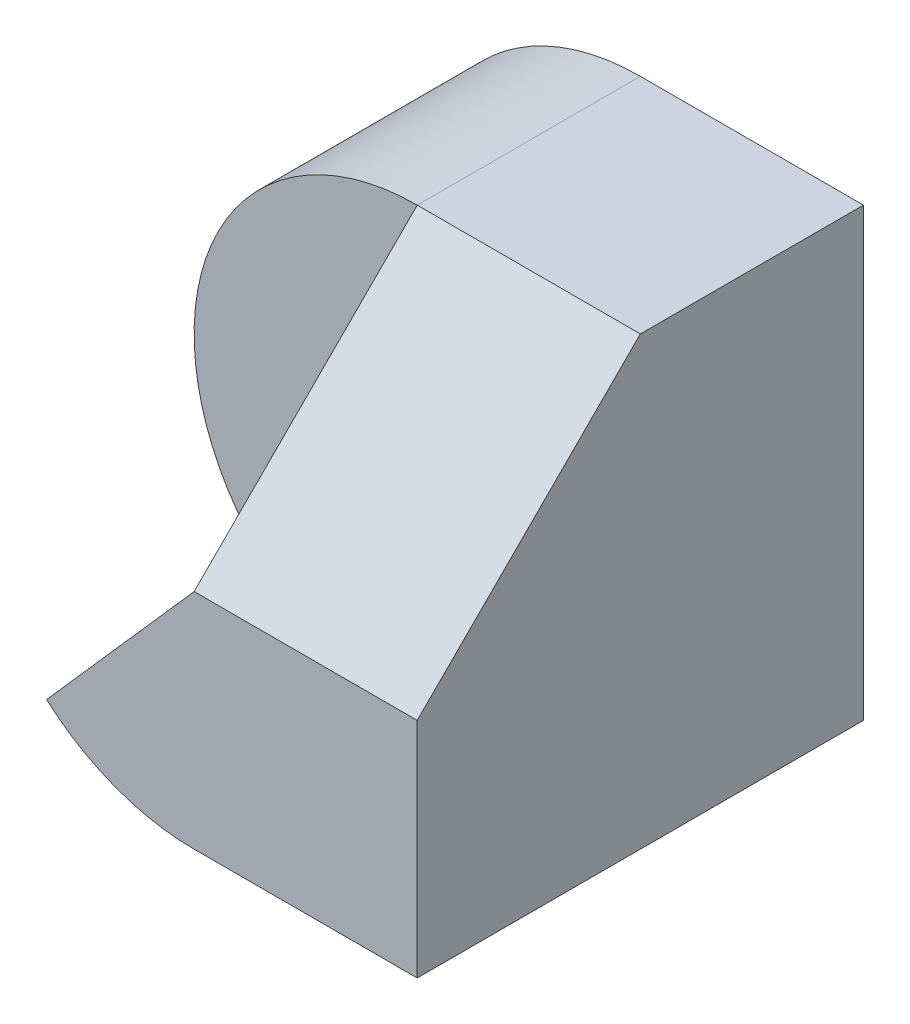
SolidWorks part; units mm, degrees
ref_plane "Front Plane" through (0, 0, 0) normal (0, 0, 1) x (1, 0, 0)
ref_plane "Top Plane" through (0, 0, 0) normal (0, 1, 0) x (1, 0, 0)
ref_plane "Right Plane" through (0, 0, 0) normal (1, 0, 0) x (0, 0, -1)
sketch "Sketch1" plane through (0, 0, 0) normal (0, 0, 1) x (1, 0, 0)
  line L1 (0, 0) -> (40, 0)
  line L2 (0, 0) -> (0, 40)
  line L3 (0, 40) -> (40, 40)
  line L4 (40, 0) -> (40, 40)
  dimension "D1" = 40
  dimension "D2" = 40
extrude "Boss-Extrude1" add sketch "Sketch1" along normal blind 40
sketch "Sketch2" plane through (0, 0, 40) normal (0, 0, 1) x (1, 0, 0)
  line L0 (0, 40) -> (0, 0) construction
  line L1 (40, 40) -> (0, 40) construction
  line L2 (20, 40) -> (0, 40)
  line L3 (0, 40) -> (0, 0)
  line L4 (0, 0) -> (20, 0)
  circle A0 centre (20, 20) radius 20
  line M1 (0, 40) -> (0, 0)
  line M2 (0, 0) -> (40, 0)
  line M4 (40, 40) -> (0, 40)
  dimension "D1" = 40
  dimension "D2" = 20
  dimension "D3" = 20
  dimension "D4" = 20
  dimension "D5" = 20
  dimension "D6" = 20
extrude "Cut-Extrude1" cut sketch "Sketch2" against normal blind 40 contours A0 M4 M1 | A0 L3 M2
ref_plane "Plane1" through (0, 40, 0) normal (0, 1, 0) x (1, 0, 0)
sketch "Sketch3" plane through (0, 40, 0) normal (0, 1, 0) x (1, 0, 0)
  line L1 (0, -40) -> (5, -40)
  line L2 (0, -40) -> (0, -20)
  line L3 (0, -20) -> (5, -20)
  line L4 (5, -40) -> (5, -20)
  dimension "D1" = 5
  dimension "D2" = 20
  dimension "D3" = 40
  dimension "D4" = 0
extrude "Cut-Extrude3" cut sketch "Sketch3" against normal blind 40
sketch "Sketch4" plane through (0, 0, 0) normal (1, 0, 0) x (0, 0, -1)
  line L0 (-20, 40) -> (-40, 20)
  line L1 (0, 0) -> (0, 40) construction
  line L3 (-20, 40) -> (-40, 40)
  line L4 (-40, 40) -> (-40, 20)
  point P2 (0, 20)
  dimension "D1" = 20
  dimension "D2" = 20
  dimension "D3" = 20
  dimension "D4" = 20
extrude "Cut-Extrude4" cut sketch "Sketch4" along normal blind 40
ref_plane "Plane2" through (0, 0, 40) normal (0, 0, 1) x (1, 0, 0)
sketch "Sketch5" plane through (0, 0, 40) normal (0, 0, 1) x (1, 0, 0)
  line L0 (40, 0) -> (40, 20) construction
  line L1 (40, 40) -> (20, 40)
  line L2 (40, 40) -> (40, 20)
  line L3 (40, 20) -> (20, 20)
  line L4 (20, 40) -> (20, 20)
  dimension "D1" = 20
  dimension "D2" = 20
  dimension "D3" = 0
  dimension "D4" = 0
extrude "Cut-Extrude6" cut sketch "Sketch5" against normal blind 20
sketch "Sketch6" plane through (0, 0, 40) normal (0, 0, 1) x (1, 0, 0)
  line L0 (20, 20) -> (6.7712, 5)
  line L1 (20, 20) -> (40, 20)
  line L2 (40, 20) -> (40, 0)
  line L3 (40, 0) -> (20, 0)
  line L4 (20, 20) -> (6.7712, 5)
  line L5 (20, 20) -> (20, 40)
  arc A0 (5, 6.7712) -> (20, 0) centre (20, 20) ccw construction
  arc A1 (20, 0) -> (6.7712, 5) centre (20, 20) cw
  arc A2 (6.7712, 5) -> (20, 40) centre (20, 20) cw
  line M2 (20, 20) -> (5, 20)
  line M3 (5, 20) -> (5, 6.7712)
  arc M4 (5, 6.7712) -> (20, 0) centre (20, 20) ccw
  dimension "D1" = 15
  dimension "D2" = 20
extrude "Cut-Extrude8" cut sketch "Sketch6" against normal blind 20 contours L0 M2 M3 M4 | A2 L5 M3 M2
sketch "Sketch7" plane through (40, 0, 0) normal (1, 0, 0) x (0, 0, -1)
  line L0 (-20, 40) -> (-40, 20)
  line L1 (-40, 20) -> (-20, 20)
  line L2 (-20, 20) -> (-20, 40)
extrude "Boss-Extrude3" add sketch "Sketch7" against normal blind 20
